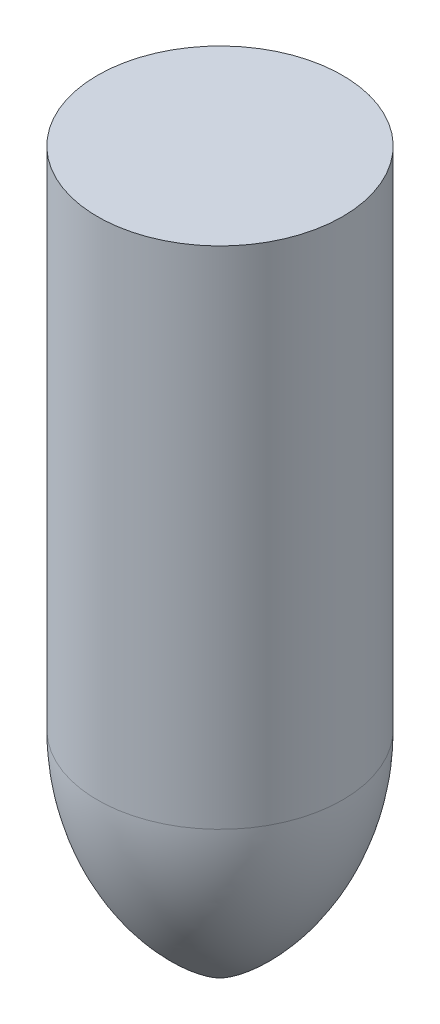
SolidWorks part; units mm, degrees
ref_plane "Front Plane" through (0, 0, 0) normal (0, 0, 1) x (1, 0, 0)
ref_plane "Top Plane" through (0, 0, 0) normal (0, 1, 0) x (1, 0, 0)
ref_plane "Right Plane" through (0, 0, 0) normal (1, 0, 0) x (0, 0, -1)
sketch "Sketch1" plane through (0, 0, 0) normal (0, 0, 1) x (1, 0, 0)
  line L0 (0, 0) -> (0, -31.75)
  line L2 (10.16, 0) -> (0, 0)
  line L3 (10.16, 0) -> (10.16, -41.91)
  line L9 (0, -31.75) -> (6.985, -31.75)
  line L10 (6.985, -31.75) -> (6.985, -46.99)
  line L11 (6.985, -46.99) -> (0, -46.99)
  line L12 (0, -46.99) -> (0, -59.69)
  arc A0 (10.16, -41.91) -> (0, -59.69) centre (-10.4775, -41.91) cw
  dimension "D1" = 10.16
  dimension "D2" = 15.24
  dimension "D4" = 6.985
  dimension "D7" = 20.32
  dimension "D8" = 19.2423
  dimension "2.35" = 59.69
  dimension "D3" = 17.78
  dimension "D5" = 31.75
  dimension "D6" = 18.1864
revolve "Revolve1" add sketch "Sketch1" angle 360 about L0
ref_plane "Plane1" through (-10.16, 0, 0) normal (-1, 0, 0) x (0, 0, 1)
sketch "Sketch2" plane through (-10.16, 0, 0) normal (-1, 0, 0) x (0, 0, 1)
  line L0 (0, -9.453) -> (0, -37.1947) construction
  line L5 (-10.16, -20.955) -> (10.16, -20.955) construction
  line L6 (-10.16, 0) -> (-10.16, -41.91) construction
  line L7 (10.16, -41.91) -> (10.16, 0) construction
  text T0 "MUDDSUB"
  point P2 (0, -6.672)
  point P4 (0, -9.6564)
  point P11 (0, -10.3347)
  point P12 (0, -8.5712)
  point P14 (0, -9.453)
  dimension "D1" = 6.35
extrude "Boss-Extrude1" add sketch "Sketch2" along normal mid plane 0.635
